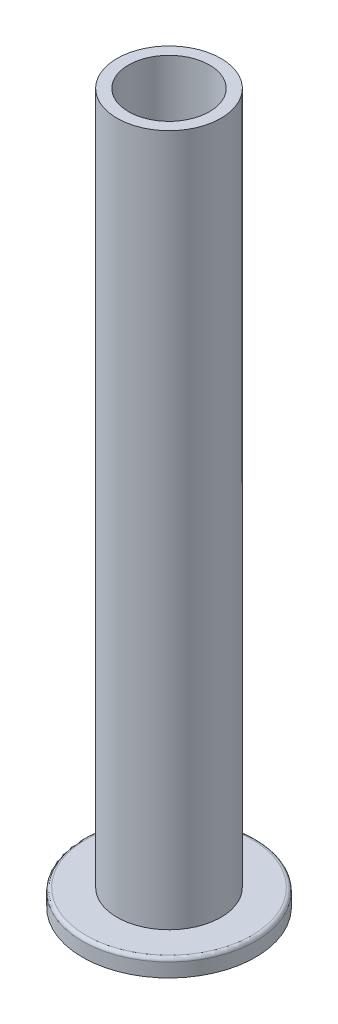
SolidWorks part; units mm, degrees
ref_plane "Front Plane" through (0, 0, 0) normal (0, 0, 1) x (1, 0, 0)
ref_plane "Top Plane" through (0, 0, 0) normal (0, 1, 0) x (1, 0, 0)
ref_plane "Right Plane" through (0, 0, 0) normal (1, 0, 0) x (0, 0, -1)
sketch "Sketch1" plane through (0, 0, 0) normal (0, 0, 1) x (1, 0, 0)
  line L0 (0, 0) -> (0, 200)
  line L1 (0, 200) -> (15, 200)
  line L2 (15, 200) -> (15, 0)
  line L4 (0, 0) -> (0, -5)
  line L9 (0, -5) -> (25, -5)
  line L10 (25, -5) -> (25, 0)
  line L11 (25, 0) -> (15, 0)
  line L12 (15, 200) -> (-15, 200) construction
  dimension "D1" = 200
  dimension "D2" = 15
  dimension "D3" = 5
  dimension "D4" = 25
revolve "Revolve1" add sketch "Sketch1" angle 360 about L0
fillet "Fillet2" radius 1 1 edges at (0, 0, -25)
sketch "Sketch2" plane through (0, 200, 0) normal (0, 1, 0) x (1, 0, 0)
  circle A0 centre (0, 0) radius 11.6966
extrude "Cut-Extrude1" cut sketch "Sketch2" against normal through all
